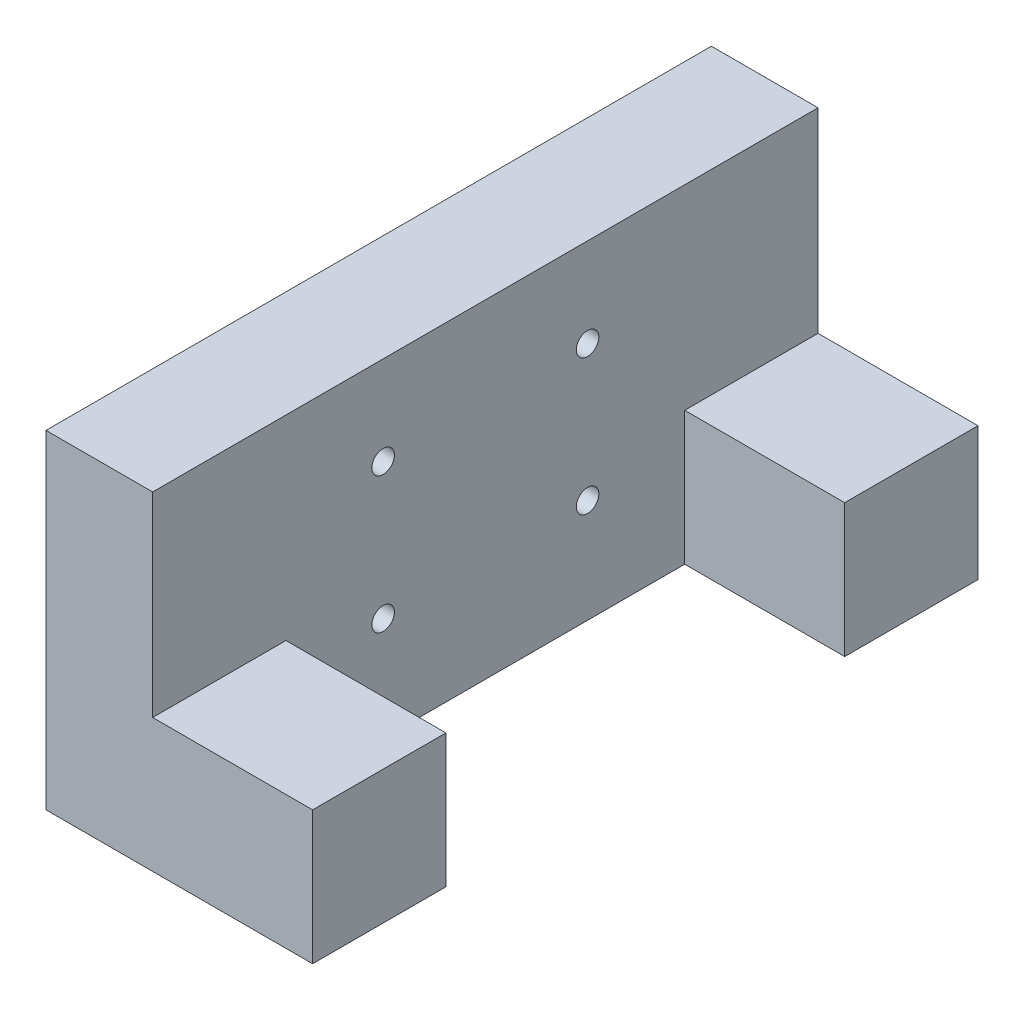
SolidWorks part; units mm, degrees
ref_plane "Front Plane" through (0, 0, 0) normal (0, 0, 1) x (1, 0, 0)
ref_plane "Top Plane" through (0, 0, 0) normal (0, 1, 0) x (1, 0, 0)
ref_plane "Right Plane" through (0, 0, 0) normal (1, 0, 0) x (0, 0, -1)
sketch "Sketch1" plane through (35.0765, 0, 0) normal (-1, 0, 0) x (0, 0, 1)
  line L1 (-320.8042, -67.476) -> (-245.9338, -67.476)
  line L2 (-320.8042, -67.476) -> (-320.8042, -104.456)
  line L3 (-320.8042, -104.456) -> (-245.9338, -104.456)
  line L4 (-245.9338, -67.476) -> (-245.9338, -104.456)
  line L6 (-300.7189, -97.476) -> (-289.7189, -97.476) construction
  line L7 (-300.7189, -67.476) -> (-289.7189, -67.476) construction
  point P0 (-283.369, -81.976)
  dimension "D1" = 6.98
extrude "Boss-Extrude1" add sketch "Sketch1" along normal blind 12
sketch "Sketch3" plane through (35.0765, 0, 0) normal (1, 0, 0) x (0, 0, -1)
  line L0 (245.9338, -67.476) -> (320.8042, -67.476) construction
  circle A0 centre (271.8689, -77.476) radius 1.27
  circle A1 centre (271.8689, -92.776) radius 1.27
  circle A2 centre (294.8689, -77.476) radius 1.27
  circle A3 centre (294.8689, -92.776) radius 1.27
  dimension "D1" = 2.54
  dimension "D2" = 10
  dimension "D3" = 15.3
  dimension "D4" = 23
  dimension "D5" = 10
sketch "Sketch4" plane through (35.0765, 0, 0) normal (1, 0, 0) x (0, 0, -1)
  line L0 (283.369, -67.476) -> (283.369, -104.456) construction
  line L1 (245.9338, -104.456) -> (260.9338, -104.456)
  line L2 (245.9338, -104.456) -> (245.9338, -89.456)
  line L3 (245.9338, -89.456) -> (260.9338, -89.456)
  line L4 (260.9338, -104.456) -> (260.9338, -89.456)
  line L5 (245.9338, -67.476) -> (320.8042, -67.476) construction
  line L6 (320.8042, -104.456) -> (245.9338, -104.456) construction
  line L7 (320.8042, -89.456) -> (305.8042, -89.456)
  line L8 (305.8042, -104.456) -> (305.8042, -89.456)
  line L9 (320.8042, -104.456) -> (305.8042, -104.456)
  line L10 (320.8042, -104.456) -> (320.8042, -89.456)
  dimension "D1" = 15
  dimension "D2" = 15
extrude "Boss-Extrude3" add sketch "Sketch4" along normal blind 18
sketch "Sketch5" plane through (0, -104.456, 0) normal (0, -1, 0) x (1, 0, 0)
  line L0 (23.0765, -283.369) -> (35.0765, -283.369) construction
  line L1 (23.0765, -320.8042) -> (23.0765, -245.9338) construction
  line L2 (35.0765, -305.8042) -> (35.0765, -260.9338) construction
  circle A0 centre (46.0265, -253.725) radius 4.075
  circle A1 centre (46.0265, -313.013) radius 4.075
  dimension "D1" = 8.15
extrude "Cut-Extrude1" cut sketch "Sketch5" against normal blind 12
sketch "Sketch6" plane through (35.0765, 0, 0) normal (1, 0, 0) x (0, 0, -1)
  circle A0 centre (269.5192, -77.4068) radius 1.27
  circle A1 centre (295.0192, -77.4068) radius 1.27
  circle A2 centre (295.0192, -95.4068) radius 1.27
  circle A3 centre (269.5192, -95.4068) radius 1.27
extrude "Cut-Extrude3" cut sketch "Sketch3" against normal through all
